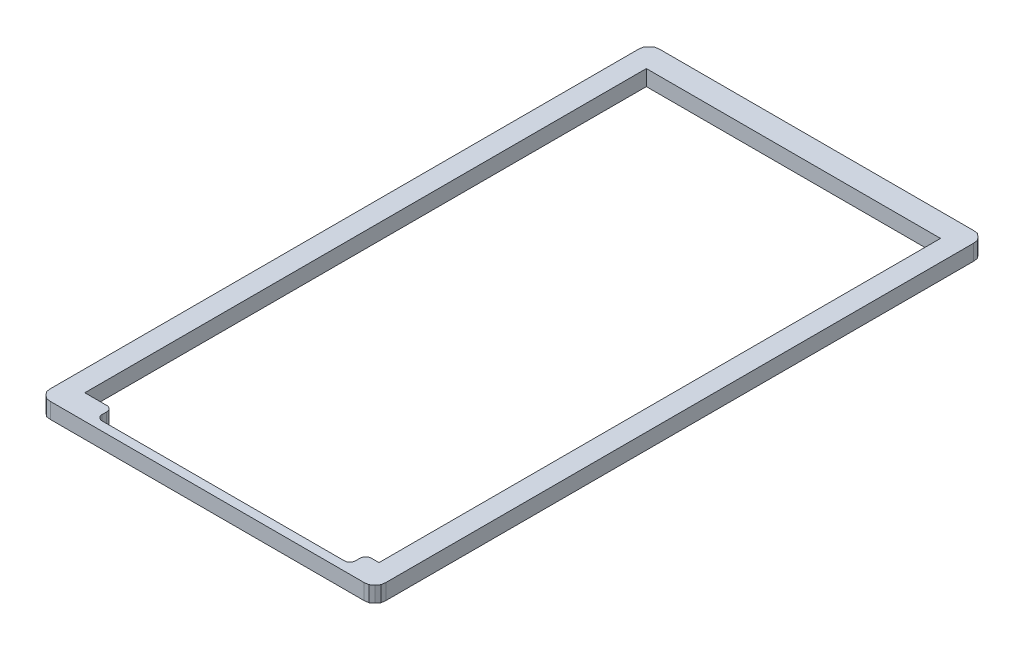
SolidWorks part; units mm, degrees
ref_plane "Ebene vorne" through (0, 0, 0) normal (0, 0, 1) x (1, 0, 0)
ref_plane "Ebene oben" through (0, 0, 0) normal (0, 1, 0) x (1, 0, 0)
ref_plane "Ebene rechts" through (0, 0, 0) normal (1, 0, 0) x (0, 0, -1)
sketch "Skizze1" plane through (0, 0, 0) normal (0, 1, 0) x (1, 0, 0)
  line L6 (11.4627, -28.4403) -> (-10.1937, -28.4403)
  line L7 (12.4627, -27.0306) -> (13.15, -27.0306)
  line L31 (11.9627, -27.5306) -> (11.9627, -27.9403)
  line L33 (-13.15, 23.1694) -> (-13.15, -27.0306)
  line L34 (13.15, 23.1694) -> (-13.15, 23.1694)
  line L35 (13.15, -27.0306) -> (13.15, 23.1694)
  line L36 (-13.15, -27.0306) -> (13.15, -27.0306)
  line L37 (-13.15, 23.1694) -> (-13.15, -27.0306)
  line L38 (13.15, 23.1694) -> (-13.15, 23.1694)
  line L39 (13.15, -27.0306) -> (13.15, 23.1694)
  line L40 (-13.15, -27.0306) -> (-11.1937, -27.0306)
  line L41 (-10.6937, -27.5306) -> (-10.6937, -27.9403)
  line L45 (14.4096, 25.2103) -> (14.0161, 25.2594)
  line L46 (14.7043, 24.9646) -> (14.4096, 25.2103)
  line L47 (14.9506, 24.6697) -> (14.7043, 24.9646)
  line L48 (14.9998, 24.2766) -> (14.9506, 24.6697)
  line L49 (14.9997, -28.2573) -> (14.9998, 24.2766)
  line L50 (14.9505, -28.6505) -> (14.9997, -28.2573)
  line L51 (14.7046, -28.9454) -> (14.9505, -28.6505)
  line L52 (14.4095, -29.1911) -> (14.7046, -28.9454)
  line L53 (14.0159, -29.2403) -> (14.4095, -29.1911)
  line L54 (-14.0169, -29.2402) -> (14.0159, -29.2403)
  line L55 (-14.4101, -29.191) -> (-14.0169, -29.2402)
  line L56 (-14.7051, -28.9456) -> (-14.4101, -29.191)
  line L57 (-14.951, -28.6504) -> (-14.7051, -28.9456)
  line L58 (-15.0002, -28.2573) -> (-14.951, -28.6504)
  line L59 (-15.0001, 24.2765) -> (-15.0002, -28.2573)
  line L60 (-14.9508, 24.6697) -> (-15.0001, 24.2765)
  line L61 (-14.7054, 24.9645) -> (-14.9508, 24.6697)
  line L62 (-14.4099, 25.2102) -> (-14.7054, 24.9645)
  line L63 (-14.0168, 25.2594) -> (-14.4099, 25.2102)
  line L64 (14.0161, 25.2594) -> (-14.0168, 25.2594)
  line L65 (14.4096, 25.2103) -> (14.0161, 25.2594)
  line L66 (14.7043, 24.9646) -> (14.4096, 25.2103)
  line L67 (14.9506, 24.6697) -> (14.7043, 24.9646)
  line L68 (14.9998, 24.2766) -> (14.9506, 24.6697)
  line L69 (14.9997, -28.2573) -> (14.9998, 24.2766)
  line L70 (14.9505, -28.6505) -> (14.9997, -28.2573)
  line L71 (14.7046, -28.9454) -> (14.9505, -28.6505)
  line L72 (14.4095, -29.1911) -> (14.7046, -28.9454)
  line L73 (14.0159, -29.2403) -> (14.4095, -29.1911)
  line L74 (-14.0169, -29.2402) -> (14.0159, -29.2403)
  line L75 (-14.4101, -29.191) -> (-14.0169, -29.2402)
  line L76 (-14.7051, -28.9456) -> (-14.4101, -29.191)
  line L77 (-14.951, -28.6504) -> (-14.7051, -28.9456)
  line L78 (-15.0002, -28.2573) -> (-14.951, -28.6504)
  line L79 (-15.0001, 24.2765) -> (-15.0002, -28.2573)
  line L80 (-14.9508, 24.6697) -> (-15.0001, 24.2765)
  line L81 (-14.7054, 24.9645) -> (-14.9508, 24.6697)
  line L82 (-14.4099, 25.2102) -> (-14.7054, 24.9645)
  line L83 (-14.0168, 25.2594) -> (-14.4099, 25.2102)
  line L84 (14.0161, 25.2594) -> (-14.0168, 25.2594)
  arc A0 (-11.1937, -27.0306) -> (-10.6937, -27.5306) centre (-11.1937, -27.5306) cw
  arc A1 (-10.1937, -28.4403) -> (-10.6937, -27.9403) centre (-10.1937, -27.9403) cw
  arc A2 (11.4627, -28.4403) -> (11.9627, -27.9403) centre (11.4627, -27.9403) ccw
  arc A3 (12.4627, -27.0306) -> (11.9627, -27.5306) centre (12.4627, -27.5306) ccw
  point P1 (0, 0)
  point P21 (11.9627, -27.0306)
  dimension "D3" = 0.5
  dimension "D1" = 0
  dimension "D2" = 0.3
extrude "Aufsatz-Linear austragen1" add sketch "Skizze1" along normal offset from surface (1.4 mm away) 0.3
